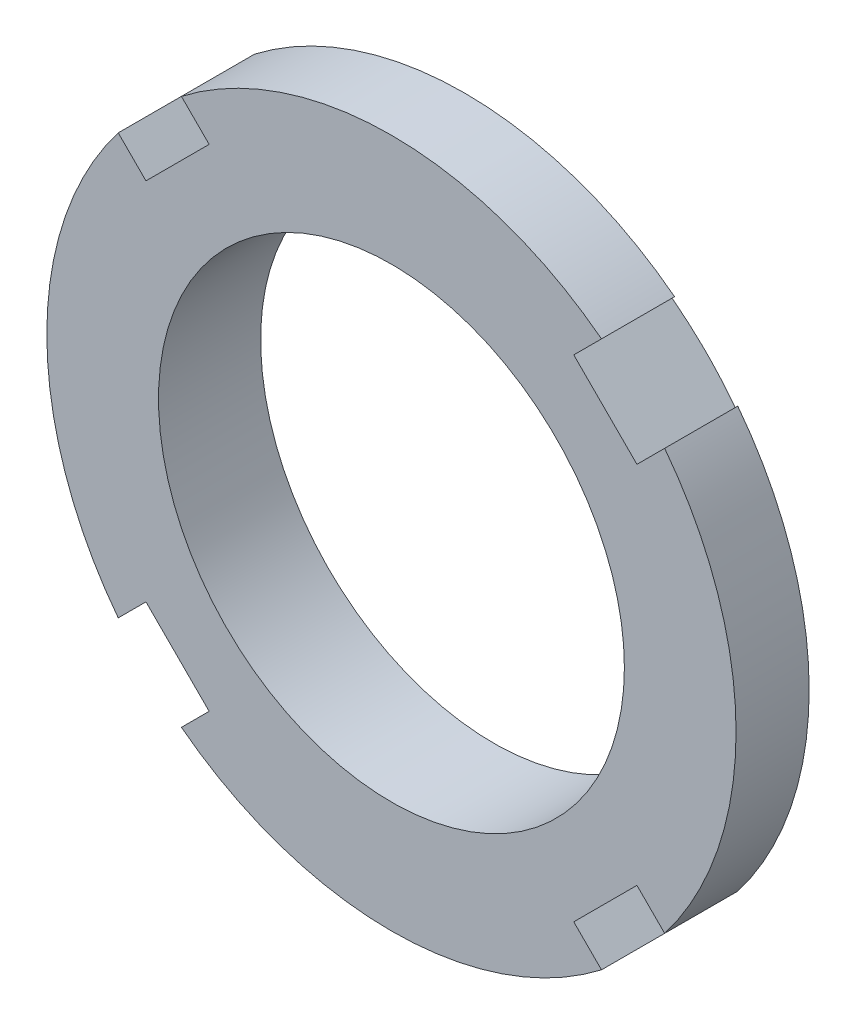
SolidWorks part; units mm, degrees
material "Alloy Steel"
ref_plane "Front Plane" through (0, 0, 0) normal (0, 0, 1) x (1, 0, 0)
ref_plane "Top Plane" through (0, 0, 0) normal (0, 1, 0) x (1, 0, 0)
ref_plane "Right Plane" through (0, 0, 0) normal (1, 0, 0) x (0, 0, -1)
sketch "Sketch1" plane through (0, 0, 0) normal (0, 0, 1) x (1, 0, 0)
  circle A0 centre (0, 0) radius 27
  circle A1 centre (0, 0) radius 18.25
  dimension "D1" = 54
  dimension "D2" = 36.5
extrude "Extrude1" add sketch "Sketch1" along normal blind 8
sketch "Sketch2" plane through (0, 0, 8) normal (0, 0, 1) x (1, 0, 0)
  line L0 (0, 0) -> (22.7176, 0) construction
  line L1 (0, 0) -> (15.6425, 15.6425) construction
  line L2 (16.4559, 21.4057) -> (14.2836, 19.2333)
  line L3 (14.2836, 19.2333) -> (19.2333, 14.2836)
  line L4 (21.4057, 16.4559) -> (19.2333, 14.2836)
  arc A1 (21.4057, 16.4559) -> (16.4559, 21.4057) centre (0, 0) ccw
  circle A3 centre (0, 0) radius 27 construction
  dimension "D3" = 23.7
  dimension "D1" = 45
  dimension "D2" = 7
extrude "Cut-Extrude1" cut sketch "Sketch2" against normal through all
pattern_circular "CirPattern1" count 4 over 360 about axis through (0, 0, 0) along (0, 0, 1) of "Cut-Extrude1"
sketch "Sketch3" plane through (0, 0, 0) normal (0, 1, 0) x (1, 0, 0)
  line L0 (27, 0) -> (21.4057, 0) construction
  line L1 (27, -8) -> (27, 0) construction
  line L2 (27, 0) -> (23.5, 0)
  line L3 (27, -2.2729) -> (27, 0)
  line L4 (23.5, 0) -> (27, -2.2729)
  line L5 (0, 0) -> (0, 7.6185) construction
  dimension "D1" = 47
  dimension "D2" = 33
revolve "Cut-Revolve1" cut sketch "Sketch3" angle 360 about L5
